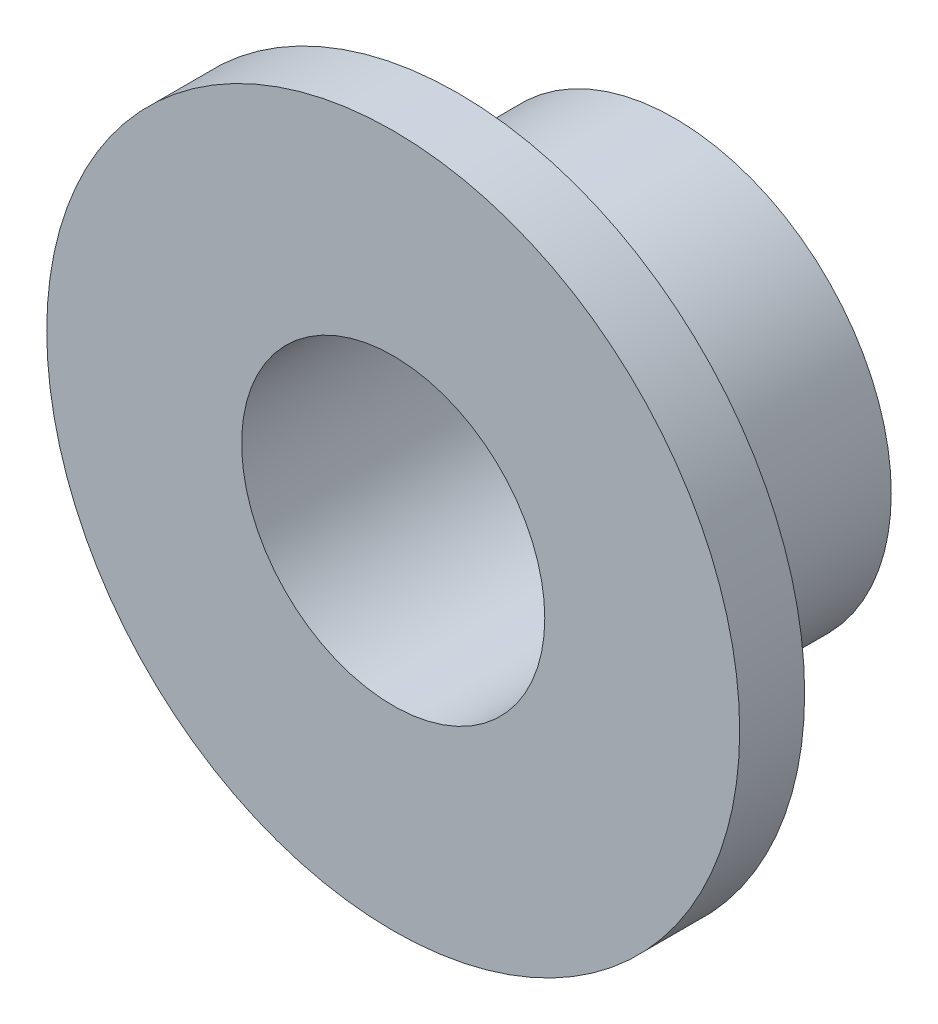
SolidWorks part; units mm, degrees
ref_plane "Front Plane" through (0, 0, 0) normal (0, 0, 1) x (1, 0, 0)
ref_plane "Top Plane" through (0, 0, 0) normal (0, 1, 0) x (1, 0, 0)
ref_plane "Right Plane" through (0, 0, 0) normal (1, 0, 0) x (0, 0, -1)
sketch "Sketch1" plane through (0, 0, 0) normal (0, 0, 1) x (1, 0, 0)
  circle A0 centre (0, 0) radius 10
  circle A1 centre (0, 0) radius 7
  dimension "D1" = 20
  dimension "D2" = 3
extrude "Boss-Extrude1" add sketch "Sketch1" along normal blind 10
sketch "Sketch2" plane through (0, 0, 10) normal (0, 0, 1) x (1, 0, 0)
  circle A0 centre (0, 0) radius 7 construction
  circle A1 centre (0, 0) radius 7
  circle A2 centre (0, 0) radius 10 construction
  circle A3 centre (0, 0) radius 10
  circle A4 centre (0, 0) radius 16
  circle A6 centre (0, 0) radius 10
  circle A7 centre (0, 0) radius 10
  circle M1 centre (0, 0) radius 10
  circle M2 centre (0, 0) radius 7
  dimension "D1" = 6
  dimension "D2" = 32
  dimension "D3" = 0
extrude "Boss-Extrude3" add sketch "Sketch2" along normal blind 3 contours A4 M1 | M1 M2
